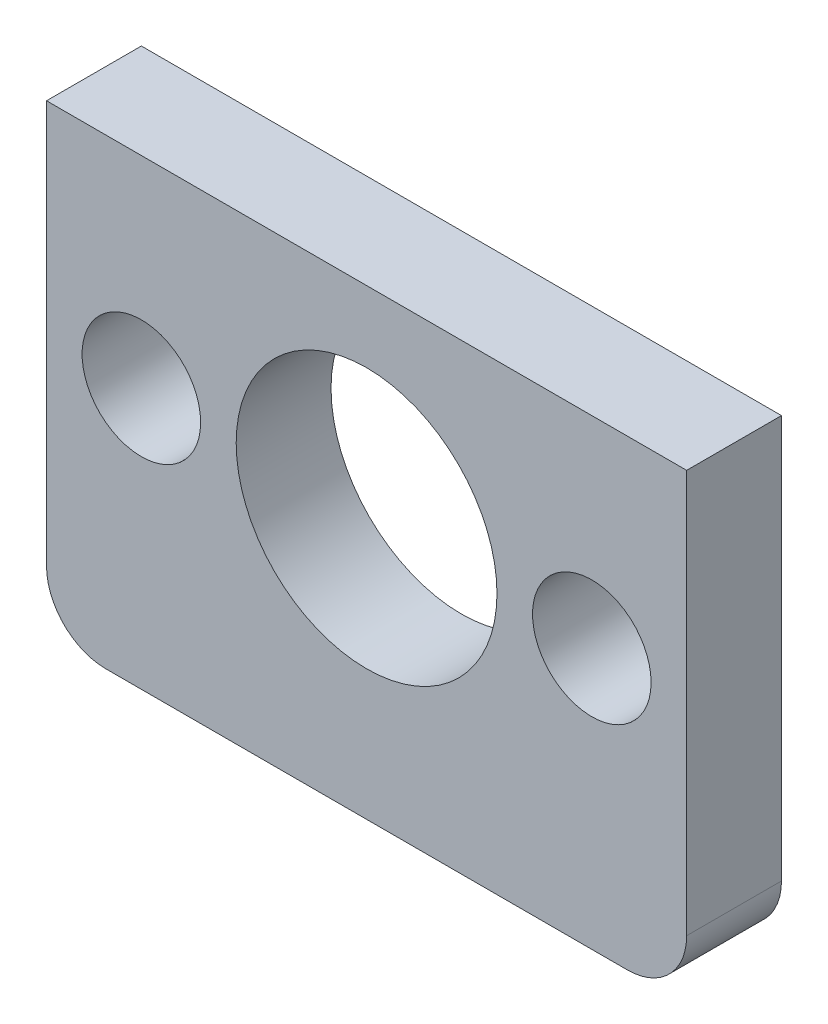
SolidWorks part; units mm, degrees
ref_plane "Front Plane" through (0, 0, 0) normal (0, 0, 1) x (1, 0, 0)
ref_plane "Top Plane" through (0, 0, 0) normal (0, 1, 0) x (1, 0, 0)
ref_plane "Right Plane" through (0, 0, 0) normal (1, 0, 0) x (0, 0, -1)
sketch "Sketch1" plane through (0, 0, 0) normal (0, 0, 1) x (1, 0, 0)
  line L1 (-22, -22) -> (22, -22)
  line L2 (-27, -17) -> (-27, 17)
  line L3 (-27, 17) -> (27, 17)
  line L4 (27, -17) -> (27, 17)
  line L5 (0, 17) -> (0, 0) construction
  line L6 (-14.2178, -17.2025) -> (14.2178, -17.2025) construction
  circle A0 centre (-19, 0) radius 5
  circle A1 centre (19, 0) radius 5
  circle A2 centre (0, 0) radius 11
  arc A6 (22, -22) -> (27, -17) centre (22, -17) ccw
  arc A7 (-22, -22) -> (-27, -17) centre (-22, -17) cw
  point P4 (0, 0)
  point P26 (27, -22)
  point P29 (-27, -22)
  dimension "D1" = 19
  dimension "D4" = 17
  dimension "D7" = 5
  dimension "D2" = 38
  dimension "D3" = 54
  dimension "D5" = 22
extrude "Boss-Extrude1" add sketch "Sketch1" along normal blind 8
